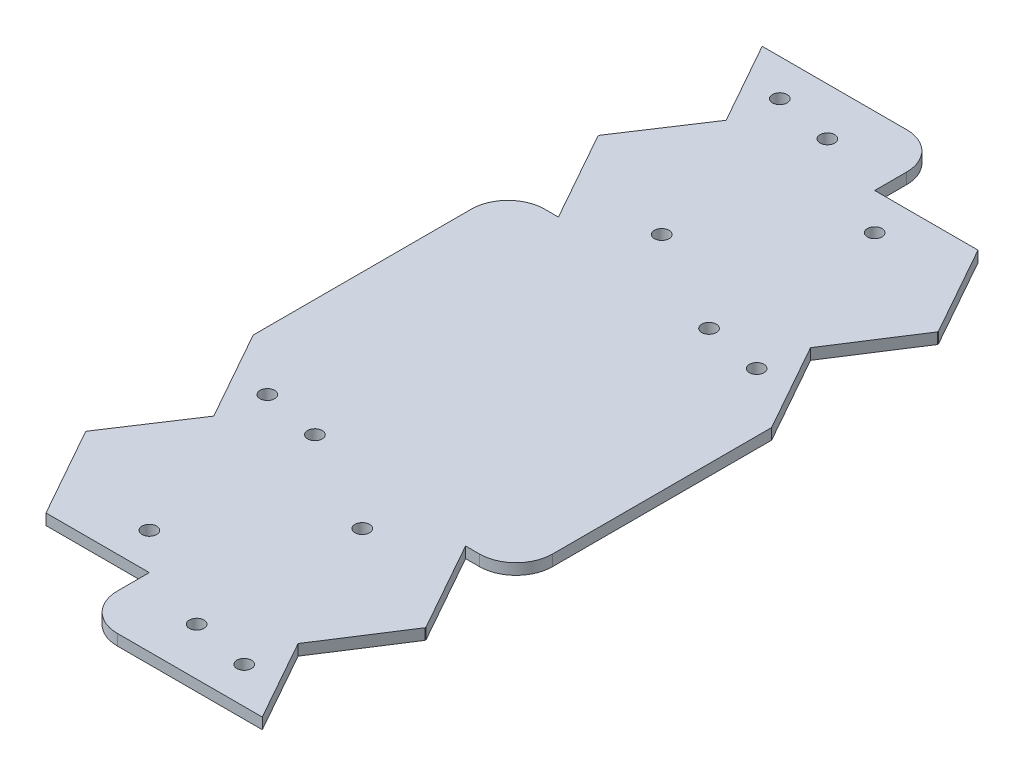
SolidWorks part; units mm, degrees
ref_plane "Front Plane" through (0, 0, 0) normal (0, 0, 1) x (1, 0, 0)
ref_plane "Top Plane" through (0, 0, 0) normal (0, 1, 0) x (1, 0, 0)
ref_plane "Right Plane" through (0, 0, 0) normal (1, 0, 0) x (0, 0, -1)
sketch "Sketch1" plane through (0, 0, 0) normal (0, 1, 0) x (1, 0, 0)
  line L0 (-4.3389, 110) -> (-46.3389, 110) construction
  line L1 (-46.35, -117) -> (46.35, -117)
  line L2 (-46.35, -117) -> (-46.35, 110)
  line L3 (-46.35, 110) -> (46.35, 110)
  line L4 (46.35, -117) -> (46.35, 110)
  line L5 (46.35, -3.5) -> (-46.35, -3.5) construction
  line L6 (4.3389, -117) -> (46.3389, -117) construction
  point P0 (0, 0)
  point P12 (0, -3.5)
  dimension "D1" = 92.7
extrude "Boss-Extrude1" add sketch "Sketch1" along normal blind 3
sketch "Sketch3" plane through (0, 0, 0) normal (0, -1, 0) x (1, 0, 0)
  line L0 (4.3389, -91.25) -> (32.5657, -91.25)
  line L1 (32.5657, -91.25) -> (46.4532, -66.5)
  line L2 (46.4532, -68) -> (46.4532, -65) construction
  line L3 (46.4532, -66.5) -> (32.7661, -45.2915)
  line L4 (32.7661, -45.2915) -> (46.35, -21.0825)
  line L5 (46.35, 117) -> (46.35, -110) construction
  line L6 (4.3389, 48.75) -> (32.5657, 48.75)
  line L7 (32.5657, 48.75) -> (46.4532, 73.5)
  line L8 (46.4532, 73.5) -> (32.7661, 94.7085)
  line L9 (32.7661, 94.7085) -> (46.35, 118.9175)
  line L10 (-46.35, 117) -> (46.35, 117) construction
  line L11 (0, 117) -> (0, -110) construction
  line L12 (46.35, -110) -> (-46.35, -110) construction
  line L13 (-4.3389, -41.75) -> (-32.5658, -41.75)
  line L14 (-32.5658, -41.75) -> (-46.4532, -66.5)
  line L16 (-46.4532, -65) -> (-46.4532, -68) construction
  line L17 (-46.4532, -66.5) -> (-32.5658, -87.576)
  line L18 (-32.5658, -87.576) -> (-46.4532, -112.326)
  line L20 (-4.3389, 98.25) -> (-32.5658, 98.25)
  line L21 (-32.5658, 98.25) -> (-46.4532, 73.5)
  line L22 (-46.4532, 73.5) -> (-32.5658, 52.424)
  line L23 (-32.5658, 52.424) -> (-46.4532, 27.674)
  line L25 (-4.3389, 98.25) -> (-4.3389, 117)
  line L26 (4.3389, -91.25) -> (4.3389, -110)
  line L27 (46.35, 118.9175) -> (46.35, 48.75)
  line L28 (46.35, 48.75) -> (32.5657, 48.75)
  line L29 (-46.4532, 27.674) -> (-46.35, 117)
  line L30 (-46.35, 117) -> (-4.3389, 117)
  line L31 (-46.4532, -112.326) -> (-46.35, -41.75)
  line L32 (-46.35, -110) -> (-46.35, 117) construction
  line L33 (-46.35, -41.75) -> (-32.5658, -41.75)
  line L34 (4.3389, -110) -> (46.35, -110)
  line L35 (46.35, -110) -> (46.35, -21.0825)
  circle A0 centre (30.3389, -33) radius 2
  circle A1 centre (14.3389, -36) radius 2
  circle A2 centre (14.3389, -81.25) radius 2
  circle A4 centre (30.3389, 107) radius 2
  circle A5 centre (14.3389, 104) radius 2
  circle A6 centre (14.3389, 58.75) radius 2
  circle A12 centre (-14.3389, -97) radius 2
  circle A13 centre (-30.3389, -100) radius 2
  circle A14 centre (-14.3389, -51.75) radius 2
  circle A15 centre (-14.3389, 43) radius 2
  circle A16 centre (-30.3389, 40) radius 2
  circle A17 centre (-14.3389, 88.25) radius 2
  line M21 (46.35, -110) -> (46.35, 117)
  line M22 (46.35, 117) -> (-46.35, 117)
  line M23 (-46.35, 117) -> (-46.35, -110)
  line M24 (-46.35, -110) -> (46.35, -110)
  dimension "D1" = 4
  dimension "D5" = 28.38
  dimension "D7" = 4
  dimension "D2" = 25.2416
  dimension "D3" = 24.209
  dimension "D6" = 68.25
  dimension "D8" = 28.38
  dimension "D9" = 25.24
  dimension "D10" = 28.38
  dimension "D12" = 69.424
  dimension "D4" = 2
  dimension "D11" = 2
extrude "Cut-Extrude1" cut sketch "Sketch3" against normal through all contours L18 L17 M23 M24 | L33 L14 M23 | A13 | A12 | L0 L26 L1 M24 M21 | L4 L3 M21 | A0 | A1 | A2 | L20 L25 L21 M22 M23 | L23 L22 M23 | L28 L7 M21 | L9 L8 M21 M22 | A6 | A5 | A4 | A15 | A16 | A17 | A14
fillet "Fillet1" radius 10 4 edges at (-4.3389, 1.5, 117) (4.3389, 1.5, -110) (-46.35, 1.5, -41.75) (46.35, 1.5, 48.75)
ref_plane "Plane1" through (0, 0, 3.5) normal (0, 0, 1) x (1, 0, 0)
